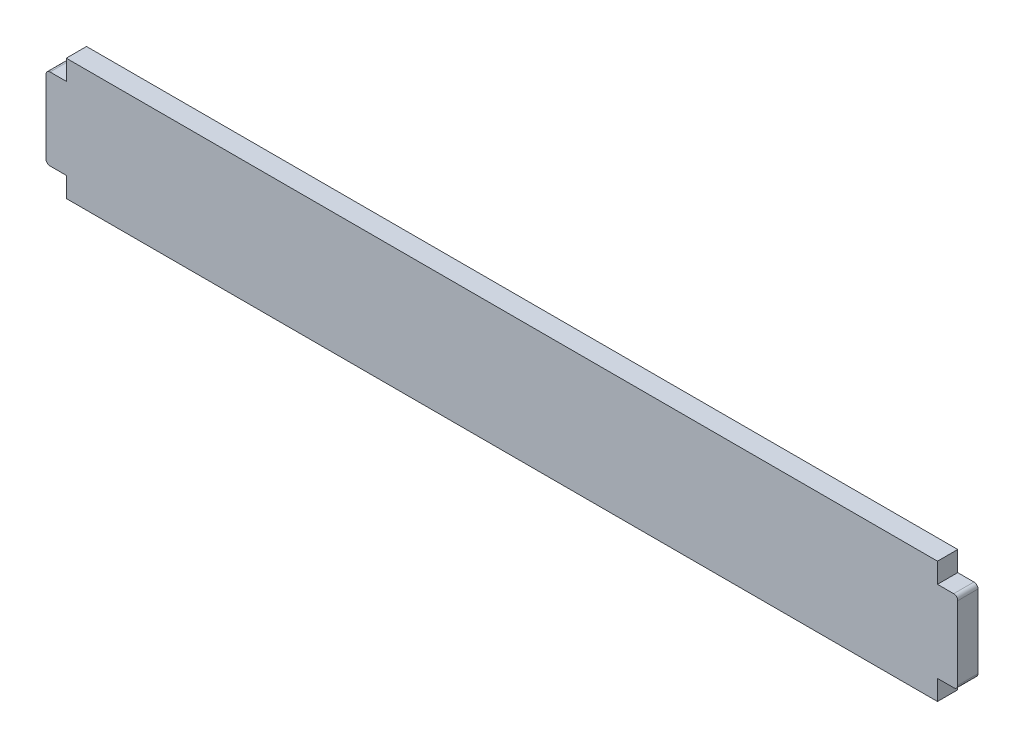
SolidWorks part; units mm, degrees
ref_plane "Front" through (0, 0, 0) normal (0, 0, 1) x (1, 0, 0)
ref_plane "Top" through (0, 0, 0) normal (0, 1, 0) x (1, 0, 0)
ref_plane "Right" through (0, 0, 0) normal (1, 0, 0) x (0, 0, -1)
sketch "Sketch1" plane through (0, 0, 0) normal (0, 0, 1) x (1, 0, 0)
  line L0 (5, 0.05) -> (220, 0.05)
  line L1 (0, 5) -> (0, 25.1)
  line L2 (225, 5) -> (225, 25.1)
  line L3 (5, 30.05) -> (220, 30.05)
  line L7 (0, 25.1) -> (5, 25.1)
  line L8 (5, 30.05) -> (5, 25.1)
  line L11 (0, 5) -> (5, 5)
  line L12 (5, 0.05) -> (5, 5)
  line L15 (225, 25.1) -> (220, 25.1)
  line L16 (220, 30.05) -> (220, 25.1)
  line L19 (225, 5) -> (220, 5)
  line L20 (220, 0.05) -> (220, 5)
  dimension "D1" = 30
  dimension "D2" = 5
  dimension "D3" = 225
  dimension "D4" = 4.95
  dimension "D5" = 4.95
  dimension "D6" = 5
  dimension "D7" = 5
  dimension "D8" = 4.95
  dimension "D9" = 5
  dimension "D10" = 4.95
extrude "Boss-Extrude1" add sketch "Sketch1" along normal blind 5
fillet "Fillet1" radius 1 4 edges at (225, 5, 2.5) (225, 25.1, 2.5) (0, 5, 2.5) (0, 25.1, 2.5)
